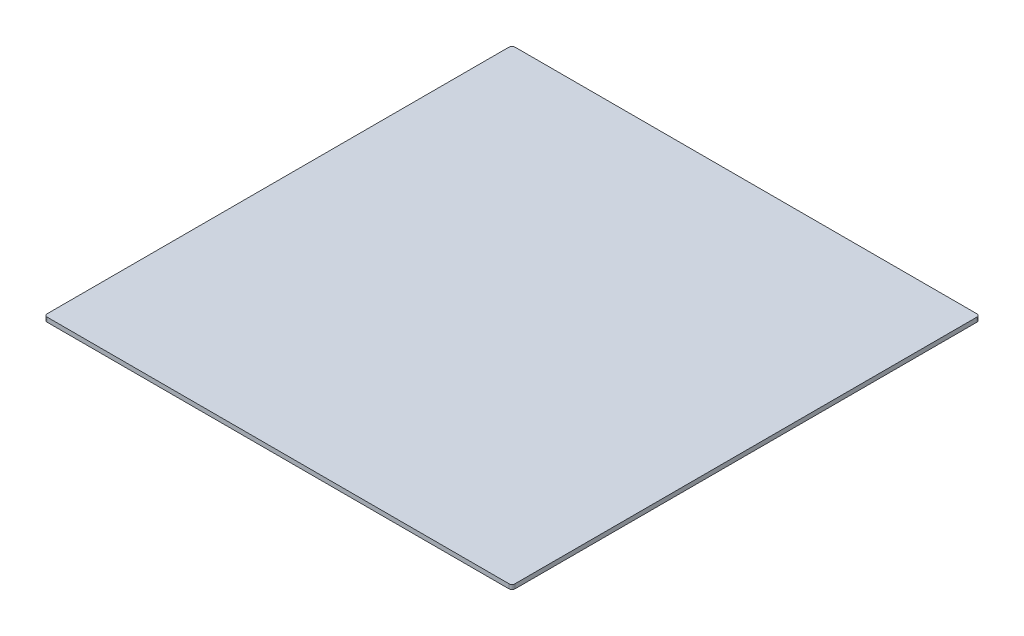
SolidWorks part; units mm, degrees
ref_plane "Front Plane" through (0, 0, 0) normal (0, 0, 1) x (1, 0, 0)
ref_plane "Top Plane" through (0, 0, 0) normal (0, 1, 0) x (1, 0, 0)
ref_plane "Right Plane" through (0, 0, 0) normal (1, 0, 0) x (0, 0, -1)
sketch "Sketch1" plane through (0, 0, 0) normal (0, 1, 0) x (1, 0, 0)
  line L1 (157.5, -157.5) -> (-157.5, -157.5)
  line L2 (157.5, -157.5) -> (157.5, 157.5)
  line L3 (157.5, 157.5) -> (-157.5, 157.5)
  line L4 (-157.5, -157.5) -> (-157.5, 157.5)
  line L5 (157.5, -157.5) -> (-157.5, 157.5) construction
  line L6 (157.5, 157.5) -> (-157.5, -157.5) construction
  point P0 (0, 0)
  dimension "D1" = 315
  dimension "D2" = 315
extrude "Boss-Extrude1" add sketch "Sketch1" along normal blind 3
fillet "Fillet1" radius 2 4 edges at (-157.5, 1.5, -157.5) (157.5, 1.5, -157.5) (157.5, 1.5, 157.5) (-157.5, 1.5, 157.5)
sketch "Sketch2" plane through (0, 0, 0) normal (0, 1, 0) x (1, 0, 0)
  line L0 (0, -212.9179) -> (0, 212.9179) construction
  line L1 (-223.4465, 0) -> (223.4465, 0) construction
  point P4 (0, 0)
  point P8 (0, 0)
